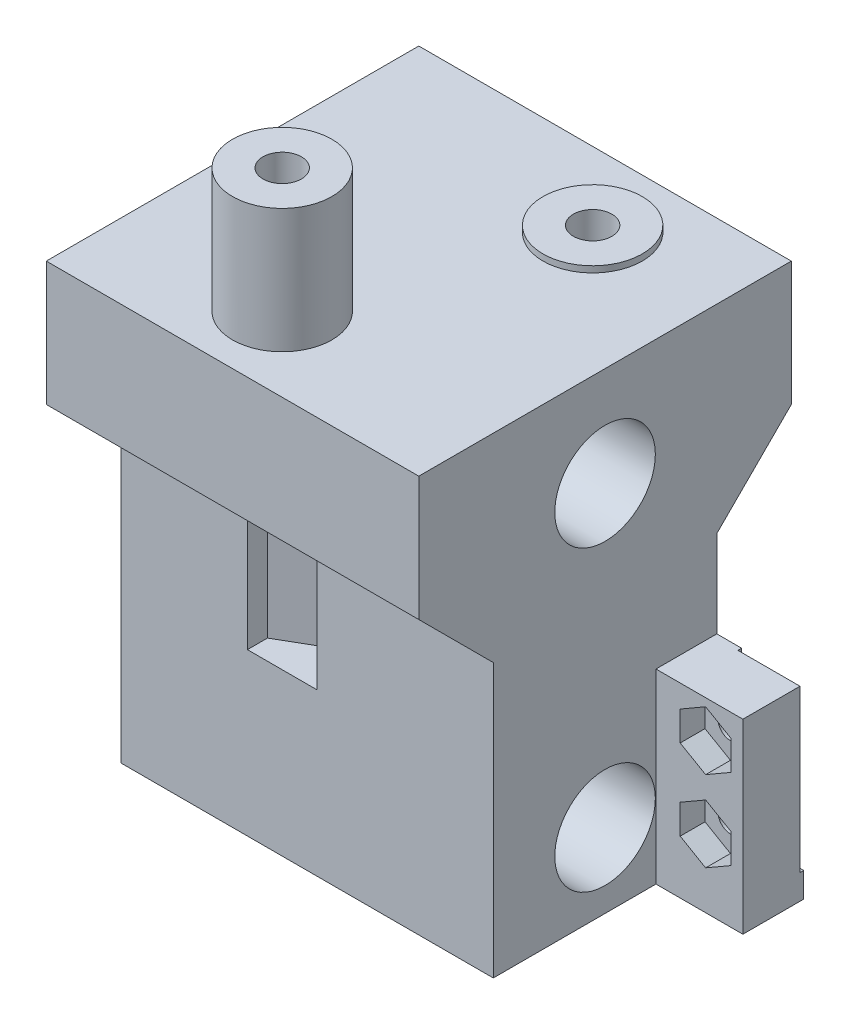
SolidWorks part; units mm, degrees
ref_plane "前视基准面" through (0, 0, 0) normal (0, 0, 1) x (1, 0, 0)
ref_plane "上视基准面" through (0, 0, 0) normal (0, 1, 0) x (1, 0, 0)
ref_plane "右视基准面" through (0, 0, 0) normal (1, 0, 0) x (0, 0, -1)
sketch "草图1" plane through (0, 0, 0) normal (0, 1, 0) x (1, 0, 0)
  line L0 (0, 0) -> (30, 0)
  line L1 (30, 0) -> (30, 30)
  line L2 (30, 30) -> (0, 30)
  line L3 (0, 30) -> (0, 0)
  dimension "D1" = 30
  dimension "D2" = 30
extrude "凸台-拉伸1" add sketch "草图1" along normal blind 38
sketch "草图3" plane through (0, 38, -50) normal (0, -1, 0) x (1, 0, 0)
  line L0 (0, 20) -> (0, 50) construction
  line L3 (30, 20) -> (0, 20) construction
  circle A0 centre (20, 26) radius 4
  dimension "D1" = 8
  dimension "D2" = 6
  dimension "D3" = 20
extrude "凸台-拉伸3" add sketch "草图3" against normal blind 0.5
sketch "草图7" plane through (0, 38, 0) normal (0, -1, 0) x (1, 0, 0)
  line L0 (0, -30) -> (0, 0) construction
  line L2 (0, 0) -> (30, 0) construction
  circle A0 centre (13, -6) radius 4
  point P6 (0, -15)
  dimension "D1" = 8
  dimension "D2" = 13
  dimension "D3" = 6
extrude "凸台-拉伸4" add sketch "草图7" against normal blind 10
ref_plane "基准面1" through (0, 28, 0) normal (0, 1, 0) x (1, 0, 0)
sketch "草图6" plane through (30, 0, 0) normal (1, 0, 0) x (0, 0, -1)
  line L0 (0, 38) -> (0, 0) construction
  line L1 (0, 0) -> (30, 0) construction
  circle A0 centre (15, 6) radius 4.05
  circle A1 centre (15, 30) radius 4.05
  dimension "D4" = 8.1
  dimension "D5" = 8.1
  dimension "D1" = 24
  dimension "D2" = 15
  dimension "D3" = 15
  dimension "D6" = 6
extrude "切除-拉伸3" cut sketch "草图6" against normal through all
sketch "草图9" plane through (0, 28, 0) normal (0, 1, 0) x (1, 0, 0)
  circle A0 centre (13, 6) radius 1.55
  circle A1 centre (20, 24) radius 1.55
  circle A2 centre (13, 6) radius 4 construction
  circle A3 centre (20, 24) radius 4 construction
  dimension "D1" = 3.1
  dimension "D2" = 3.1
extrude "切除-拉伸4" cut sketch "草图9" along normal through all
sketch "草图11" plane through (30, 0, 0) normal (1, 0, 0) x (0, 0, -1)
  line L0 (6, 0) -> (6, 22)
  line L1 (0, 0) -> (30, 0) construction
  line L2 (24, 0) -> (24, 22)
  line L3 (24, 22) -> (30, 28)
  line L4 (16.5, 28) -> (-16.5, 28) construction
  line L5 (30, 38) -> (30, 0) construction
  line L6 (30, 28) -> (30, 0)
  line L7 (30, 0) -> (24, 0)
  line L8 (6, 0) -> (0, 0)
  line L9 (0, 0) -> (0, 28)
  line L10 (0, 38) -> (0, 0) construction
  line L11 (0, 28) -> (6, 22)
  dimension "D1" = 45
  dimension "D2" = 45
  dimension "D3" = 6
  dimension "D4" = 6
extrude "切除-拉伸6" cut sketch "草图11" against normal through all
sketch "草图10" plane through (0, 28, 0) normal (0, 1, 0) x (1, 0, 0)
  line L0 (0, 0) -> (30, 0) construction
  line L1 (15.8, 0) -> (15.8, 7.6166)
  line L2 (15.8, 7.6166) -> (13, 9.2332)
  line L3 (13, 9.2332) -> (10.2, 7.6166)
  line L4 (10.2, 7.6166) -> (10.2, 0)
  line L7 (20, 20.7668) -> (22.8, 22.3834)
  line L8 (22.8, 22.3834) -> (22.8, 30)
  line L11 (17.2, 30) -> (17.2, 22.3834)
  line L12 (17.2, 22.3834) -> (20, 20.7668)
  line L14 (30, 0) -> (30, 30) construction
  line L15 (30, 30) -> (0, 30) construction
  line L16 (0, 30) -> (0, 0) construction
  line L17 (10.2, 4.3834) -> (13, 2.7668) [skipped]
  line L18 (13, 2.7668) -> (15.8, 4.3834) [skipped]
  line L19 (22.8, 25.6166) -> (20, 27.2332) [skipped]
  line L20 (20, 27.2332) -> (17.2, 25.6166) [skipped]
  line L21 (17.2, 30) -> (22.8, 30)
  line L22 (10.2, 0) -> (15.8, 0)
  circle A0 centre (13, 6) radius 2.8 construction
  circle A1 centre (20, 24) radius 2.8 construction
  circle A2 centre (20, 24) radius 1.55 construction
  circle A3 centre (13, 6) radius 1.55 construction
  dimension "D5" = 5.6
  dimension "D6" = 5.6
extrude "切除-拉伸5" cut sketch "草图10" against normal blind 15
sketch "草图12" plane through (30, 0, 0) normal (1, 0, 0) x (0, 0, -1)
  line L0 (19.1, 15) -> (19.1, 0)
  line L2 (19.1, 15) -> (24, 15)
  line L5 (24, 15) -> (24, 0)
  line L7 (24, 22) -> (24, 0) construction
  line L12 (0, 38) -> (0, 28)
  line L14 (0, 28) -> (6, 22)
  line L15 (6, 0) -> (24, 0)
  line L16 (6, 22) -> (6, 0)
  line L17 (24, 0) -> (24, 22)
  line L18 (30, 28) -> (30, 38)
  line L19 (30, 38) -> (0, 38)
  line L23 (19.1, 0) -> (24, 0)
  line L29 (24, 22) -> (30, 28)
  dimension "D2" = 15
  dimension "D3" = 4.9
  dimension "D1" = 0
extrude "凸台-拉伸5" add sketch "草图12" along normal blind 7
sketch "草图13" plane through (0, 0, -24) normal (0, 0, -1) x (-1, 0, 0)
  line L0 (-32, 15) -> (-32, 2)
  line L2 (-32, 2) -> (-37, 2)
  line L4 (-37, 2) -> (-37, 15)
  line L5 (-37, 15) -> (-32, 15)
  dimension "D1" = 5
  dimension "D2" = 13
extrude "切除-拉伸7" cut sketch "草图13" against normal blind 0.3
sketch "草图14" plane through (0, 0, -23.7) normal (0, 0, -1) x (-1, 0, 0)
  line L0 (-37, 15) -> (-37, 2) construction
  line L1 (-32, 15) -> (-37, 15) construction
  circle A0 centre (-34, 12) radius 1
  circle A1 centre (-34, 5.5) radius 1
  dimension "D1" = 2
  dimension "D2" = 2
  dimension "D3" = 3
  dimension "D4" = 3
  dimension "D5" = 3
  dimension "D6" = 6.5
extrude "切除-拉伸8" cut sketch "草图14" against normal through all
sketch "草图15" plane through (0, 0, -19.1) normal (0, 0, 1) x (1, 0, 0)
  line L0 (37, 15) -> (37, 0) construction
  line L1 (36.05, 10.8164) -> (36.05, 13.1836)
  line L2 (36.05, 13.1836) -> (34, 14.3671)
  line L3 (34, 14.3671) -> (31.95, 13.1836)
  line L4 (31.95, 13.1836) -> (31.95, 10.8164)
  line L5 (31.95, 10.8164) -> (34, 9.6329)
  line L6 (34, 9.6329) -> (36.05, 10.8164)
  line L7 (37, 15) -> (37, 0) construction
  line L8 (34, 3.1329) -> (36.05, 4.3164)
  line L9 (36.05, 4.3164) -> (36.05, 6.6836)
  line L10 (36.05, 6.6836) -> (34, 7.8671)
  line L11 (34, 7.8671) -> (31.95, 6.6836)
  line L12 (31.95, 6.6836) -> (31.95, 4.3164)
  line L13 (31.95, 4.3164) -> (34, 3.1329)
  circle A0 centre (34, 12) radius 2.05 construction
  circle A1 centre (34, 5.5) radius 2.05 construction
  dimension "D1" = 4.1
  dimension "D2" = 4.1
extrude "切除-拉伸9" cut sketch "草图15" against normal blind 2
